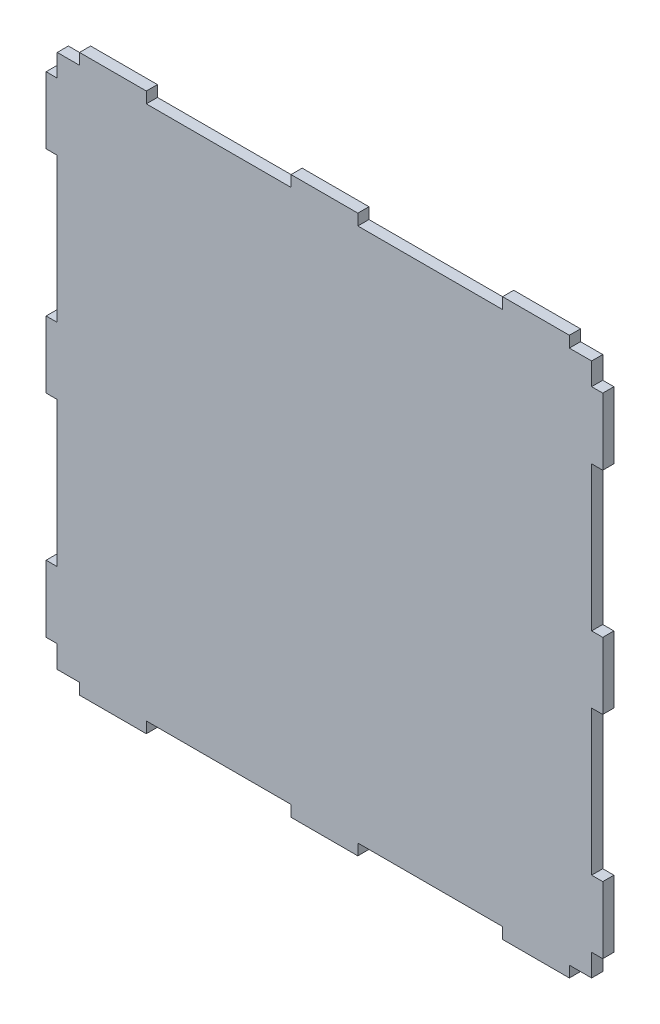
SolidWorks part; units mm, degrees
ref_plane "Front Plane" through (0, 0, 0) normal (0, 0, 1) x (1, 0, 0)
ref_plane "Top Plane" through (0, 0, 0) normal (0, 1, 0) x (1, 0, 0)
ref_plane "Right Plane" through (0, 0, 0) normal (1, 0, 0) x (0, 0, -1)
sketch "Sketch1" plane through (0, 0, 0) normal (0, 0, 1) x (1, 0, 0)
  line L1 (-120, 120) -> (120, 120)
  line L2 (-120, 120) -> (-120, -120)
  line L3 (-120, -120) -> (120, -120)
  line L4 (120, 120) -> (120, -120)
  line L5 (-120, 120) -> (120, -120) construction
  line L6 (-120, -120) -> (120, 120) construction
  line L7 (-110, 120) -> (-80, 120)
  line L8 (-110, 120) -> (-110, 125)
  line L9 (-110, 125) -> (-80, 125)
  line L10 (-80, 120) -> (-80, 125)
  line L11 (-15, 120) -> (15, 120)
  line L12 (-15, 120) -> (-15, 125)
  line L13 (-15, 125) -> (15, 125)
  line L14 (15, 120) -> (15, 125)
  line L15 (80, 120) -> (110, 120)
  line L16 (80, 120) -> (80, 125)
  line L17 (80, 125) -> (110, 125)
  line L18 (110, 120) -> (110, 125)
  line L19 (120, 110) -> (125, 110)
  line L20 (120, 110) -> (120, 80)
  line L21 (120, 80) -> (125, 80)
  line L22 (125, 110) -> (125, 80)
  line L23 (120, 15) -> (125, 15)
  line L24 (120, 15) -> (120, -15)
  line L25 (120, -15) -> (125, -15)
  line L26 (125, 15) -> (125, -15)
  line L27 (120, -80) -> (125, -80)
  line L28 (120, -80) -> (120, -110)
  line L29 (120, -110) -> (125, -110)
  line L30 (125, -80) -> (125, -110)
  line L31 (110, -120) -> (80, -120)
  line L32 (110, -120) -> (110, -125)
  line L33 (110, -125) -> (80, -125)
  line L34 (80, -120) -> (80, -125)
  line L35 (15, -120) -> (-15, -120)
  line L36 (15, -120) -> (15, -125)
  line L37 (15, -125) -> (-15, -125)
  line L38 (-15, -120) -> (-15, -125)
  line L39 (-80, -120) -> (-110, -120)
  line L40 (-80, -120) -> (-80, -125)
  line L41 (-80, -125) -> (-110, -125)
  line L42 (-110, -120) -> (-110, -125)
  line L43 (-120, -110) -> (-125, -110)
  line L44 (-120, -110) -> (-120, -80)
  line L45 (-120, -80) -> (-125, -80)
  line L46 (-125, -110) -> (-125, -80)
  line L47 (-120, -15) -> (-125, -15)
  line L48 (-120, -15) -> (-120, 15)
  line L49 (-120, 15) -> (-125, 15)
  line L50 (-125, -15) -> (-125, 15)
  line L51 (-120, 80) -> (-125, 80)
  line L52 (-120, 80) -> (-120, 110)
  line L53 (-120, 110) -> (-125, 110)
  line L54 (-125, 80) -> (-125, 110)
  point P0 (0, 0)
  dimension "D1" = 240
  dimension "D2" = 240
  dimension "D4" = 30
  dimension "D5" = 5
  dimension "D6" = 10
  dimension "D7" = 65
  dimension "D8" = 30
  dimension "D9" = 5
  dimension "D10" = 65
  dimension "D11" = 30
  dimension "D12" = 5
  dimension "D13" = 5
  dimension "D14" = 30
  dimension "D15" = 30
  dimension "D16" = 30
  dimension "D17" = 5
  dimension "D18" = 5
  dimension "D19" = 65
  dimension "D20" = 10
  dimension "D21" = 65
  dimension "D22" = 30
  dimension "D23" = 5
  dimension "D24" = 5
  dimension "D25" = 5
  dimension "D26" = 30
  dimension "D27" = 30
  dimension "D28" = 10
  dimension "D29" = 65
  dimension "D30" = 65
  dimension "D31" = 30
  dimension "D32" = 30
  dimension "D33" = 30
  dimension "D34" = 5
  dimension "D35" = 5
  dimension "D36" = 5
  dimension "D37" = 10
  dimension "D38" = 65
  dimension "D39" = 65
sketch "Sketch2" plane through (0, 0, 0) normal (0, 0, 1) x (1, 0, 0)
  line L0 (-120, 120) -> (120, 120)
  line L1 (120, 120) -> (120, -120)
  line L2 (120, -120) -> (-120, -120)
  line L3 (-120, -120) -> (-120, 120)
  line L4 (-15, 120) -> (-15, 125)
  line L5 (-15, 125) -> (15, 125)
  line L6 (15, 125) -> (15, 120)
  line L7 (80, 120) -> (80, 125)
  line L8 (80, 125) -> (110, 125)
  line L9 (110, 125) -> (110, 120)
  line L10 (-110, 120) -> (-110, 125)
  line L11 (-110, 125) -> (-80, 125)
  line L12 (-80, 125) -> (-80, 120)
  line L13 (-120, 80) -> (-125, 80)
  line L14 (-125, 80) -> (-125, 110)
  line L15 (-125, 110) -> (-120, 110)
  line L16 (-120, -15) -> (-125, -15)
  line L17 (-125, -15) -> (-125, 15)
  line L18 (-125, 15) -> (-120, 15)
  line L19 (-120, -110) -> (-125, -110)
  line L20 (-125, -110) -> (-125, -80)
  line L21 (-125, -80) -> (-120, -80)
  line L22 (-110, -120) -> (-110, -125)
  line L23 (-110, -125) -> (-80, -125)
  line L24 (-80, -125) -> (-80, -120)
  line L25 (-15, -120) -> (-15, -125)
  line L26 (-15, -125) -> (15, -125)
  line L27 (15, -125) -> (15, -120)
  line L28 (80, -120) -> (80, -125)
  line L29 (80, -125) -> (110, -125)
  line L30 (110, -125) -> (110, -120)
  line L31 (120, -110) -> (125, -110)
  line L32 (125, -110) -> (125, -80)
  line L33 (125, -80) -> (120, -80)
  line L34 (120, -15) -> (125, -15)
  line L35 (125, -15) -> (125, 15)
  line L36 (125, 15) -> (120, 15)
  line L37 (120, 80) -> (125, 80)
  line L38 (125, 80) -> (125, 110)
  line L39 (125, 110) -> (120, 110)
extrude "Boss-Extrude1" add sketch "Sketch1" along normal blind 5 contours L4 L1 L2 L3 | L1 L14 L13 L12 | L1 L18 L17 L16 | L54 L51 L2 L53 | L50 L47 L2 L49 | L46 L43 L2 L45 | L3 L42 L41 L40 | L3 L38 L37 L36 | L3 L34 L33 L32 | L30 L27 L4 L29 | L26 L23 L4 L25 | L22 L19 L4 L21 | L9 L10 L7 L8
